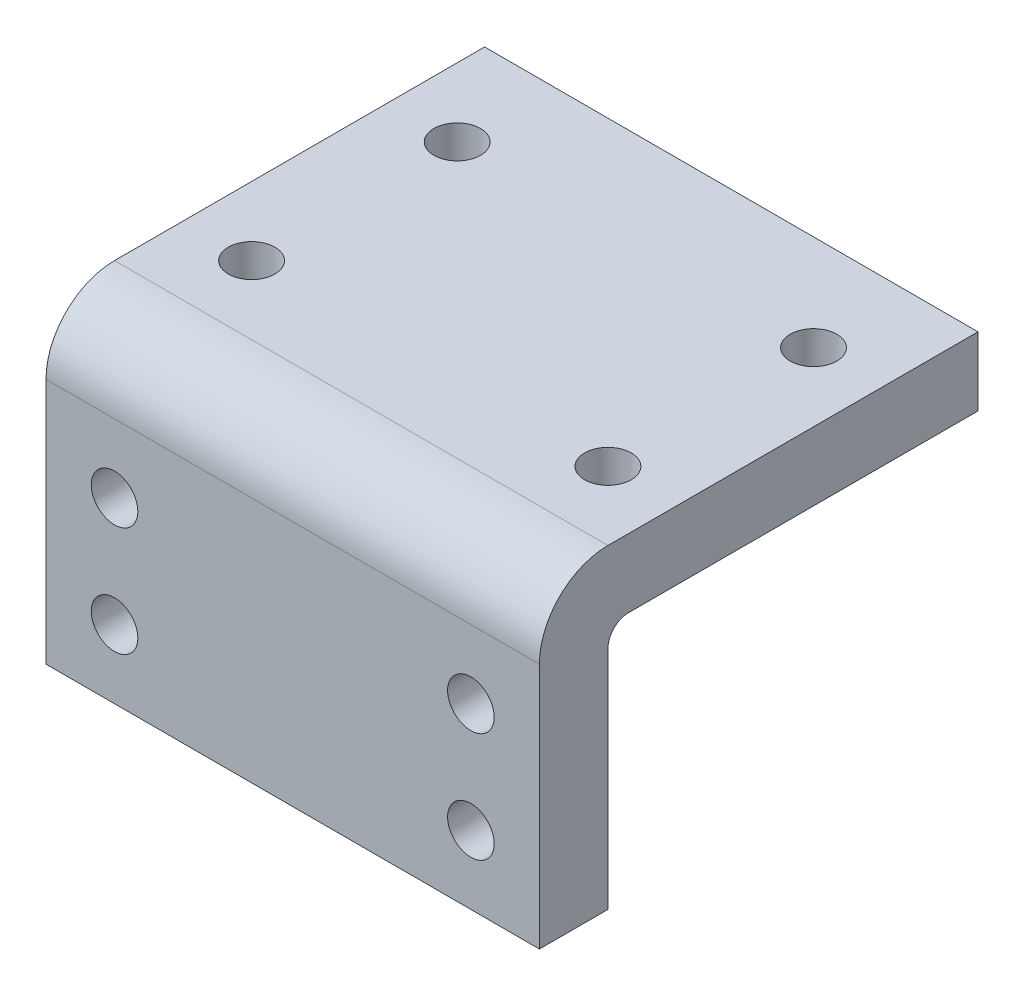
SolidWorks part; units mm, degrees
ref_plane "Front Plane" through (0, 0, 0) normal (0, 0, 1) x (1, 0, 0)
ref_plane "Top Plane" through (0, 0, 0) normal (0, 1, 0) x (1, 0, 0)
ref_plane "Right Plane" through (0, 0, 0) normal (1, 0, 0) x (0, 0, -1)
sketch "Sketch1" plane through (0, 0, 0) normal (0, 0, 1) x (1, 0, 0)
  line L0 (0, 0) -> (36, 0)
  line L1 (36, 0) -> (36, 18)
  line L2 (36, 18) -> (0, 18)
  line L3 (0, 18) -> (0, 0)
  line L4 (18, 18) -> (18, 0) construction
  circle A0 centre (31, 5) radius 1.5 construction
  circle A1 centre (31, 13) radius 1.5 construction
  circle A2 centre (5, 5) radius 1.5 construction
  circle A3 centre (5, 13) radius 1.5 construction
  dimension "D3" = 3
  dimension "D1" = 36
  dimension "D2" = 18
  dimension "D4" = 5
  dimension "D5" = 5
  dimension "D7" = 5
  dimension "D6" = 2
extrude "Boss-Extrude1" add sketch "Sketch1" along normal blind 5
hole_wizard "CSK for M3 Flat Head Machine Screw1" positions "Sketch5" profile "Sketch6" countersink size "M3" standard "ANSI Metric" end condition up to next
sketch "Sketch5" plane through (0, 0, 0) normal (0, 0, -1) x (-1, 0, 0)
  point P0 (-31, 13)
  point P3 (-31, 5)
  point P6 (-5, 5)
  point P9 (-5, 13)
sketch "Sketch6" plane through (31, 13, 0) normal (1, 0, 0) x (0, 1, 0)
  line L0 (0, 0) -> (0, 5)
  line L1 (0, 5) -> (1.7, 5)
  line L2 (1.7, 5) -> (1.7, 1.45)
  line L3 (1.7, 1.45) -> (3.15, 0)
  line L5 (3.15, 0) -> (0, 0)
  line L6 (-1.7, 1.45) -> (-3.15, 0) construction
  line L11 (0, -6.35) -> (0, 107.95) construction
  dimension "Thru Hole Dia." = 3.4
  dimension "Thru Hole Depth" = 5
  dimension "Near C'Sink Dia." = 6.3
  dimension "Near C'Sink Angle" = 90
sketch "Sketch7" plane through (0, 18, 0) normal (0, 1, 0) x (1, 0, 0)
  line L0 (0, -5) -> (0, 27)
  line L1 (0, 27) -> (36, 27)
  line L2 (36, 27) -> (36, -5)
  line L3 (36, -5) -> (0, -5)
  line L4 (18, -5) -> (18, 27) construction
  circle A0 centre (31, 5) radius 1.5 construction
  circle A1 centre (31, 20) radius 1.5 construction
  circle A2 centre (5, 20) radius 1.5 construction
  circle A3 centre (5, 5) radius 1.5 construction
  dimension "D2" = 3
  dimension "D5" = 3
  dimension "D1" = 32
  dimension "D3" = 10
  dimension "D4" = 5
  dimension "D6" = 5
  dimension "D7" = 25
extrude "Boss-Extrude2" add sketch "Sketch7" along normal blind 5
hole_wizard "CSK for M3 Flat Head Machine Screw2" positions "Sketch10" profile "Sketch11" countersink size "M3" standard "ANSI Metric" end condition up to next
sketch "Sketch10" plane through (0, 18, 0) normal (0, -1, 0) x (-1, 0, 0)
  point P0 (-31, 5)
  point P3 (-31, 20)
  point P6 (-5, 20)
  point P9 (-5, 5)
sketch "Sketch11" plane through (31, 18, -5) normal (1, 0, 0) x (0, 0, -1)
  line L0 (0, 0) -> (0, 5)
  line L1 (0, 5) -> (1.7, 5)
  line L2 (1.7, 5) -> (1.7, 1.45)
  line L3 (1.7, 1.45) -> (3.15, 0)
  line L5 (3.15, 0) -> (0, 0)
  line L6 (-1.7, 1.45) -> (-3.15, 0) construction
  line L11 (0, -6.35) -> (0, 107.95) construction
  dimension "Thru Hole Dia." = 3.4
  dimension "Thru Hole Depth" = 5
  dimension "Near C'Sink Dia." = 6.3
  dimension "Near C'Sink Angle" = 90
fillet "Fillet1" radius 1.5 1 edges at (18, 18, 0)
fillet "Fillet2" radius 5 1 edges at (18, 23, 5)
